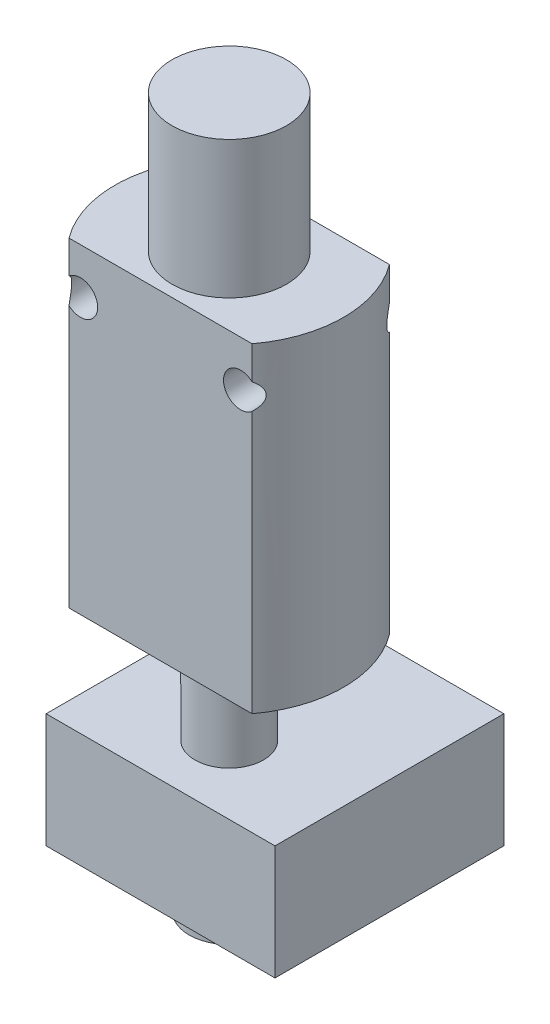
SolidWorks part; units mm, degrees
ref_plane "Plano frontal" through (0, 0, 0) normal (0, 0, 1) x (1, 0, 0)
ref_plane "Plano superior" through (0, 0, 0) normal (0, 1, 0) x (1, 0, 0)
ref_plane "Plano direito" through (0, 0, 0) normal (1, 0, 0) x (0, 0, -1)
sketch "Esboço1" plane through (0, 0, 0) normal (0, 0, 1) x (1, 0, 0)
  line L0 (0, 0) -> (0, 24.6707) construction
  line L2 (-10, 14) -> (10, 14)
  line L3 (-10, 14) -> (-10, -14)
  line L4 (-10, -14) -> (10, -14)
  line L5 (10, 14) -> (10, -14)
  line L6 (-10, 14) -> (10, -14) construction
  line L7 (-10, -14) -> (10, 14) construction
  circle A0 centre (-7, 10) radius 1.5
  circle A1 centre (7, 10) radius 1.5
  point P3 (0, 0)
  dimension "D4" = 3
  dimension "D1" = 28
  dimension "D2" = 20
  dimension "D3" = 14
  dimension "D5" = 4
extrude "Ressalto-extrusão1" add sketch "Esboço1" along normal mid plane 12
sketch "Esboço2" plane through (0, 0, 0) normal (0, 0, 1) x (1, 0, 0)
  line L0 (0, 0) -> (0, -38) construction
  line L1 (3, -33) -> (3, -23)
  line L3 (3, -33) -> (3.5, -33)
  line L4 (3.5, -33) -> (3.5, -36)
  line L5 (3.5, -36) -> (0.75, -38)
  line L6 (0.75, -38) -> (0, -38)
  line L7 (10, 14) -> (-10, 14) construction
  line L8 (3, -23) -> (3, -14)
  line L9 (-10, -14) -> (10, -14) construction
  line L10 (0, -38) -> (0, -14)
  line L11 (3, -14) -> (0, -14)
  line L12 (0, 26) -> (5, 26)
  line L13 (5, 26) -> (5, 14)
  line L14 (5, 14) -> (0, 14)
  line L15 (0, 26) -> (0, 14)
  dimension "D1" = 2
  dimension "D2" = 9
  dimension "D3" = 10
  dimension "D4" = 6
  dimension "D5" = 3
  dimension "D6" = 7
  dimension "D7" = 1.5
  dimension "D8" = 12
  dimension "D9" = 10
revolve "Revolução1" add sketch "Esboço2" angle 360 about L0
sketch "Esboço3" plane through (0, 0, 0) normal (0, 1, 0) x (1, 0, 0)
  line L0 (10, -6) -> (-10, -6) construction
  line L1 (-10, 14) -> (10, 14)
  line L2 (-10, 14) -> (-10, -6)
  line L3 (-10, -6) -> (10, -6)
  line L4 (10, 14) -> (10, -6)
  line L5 (-10, 14) -> (10, -6) construction
  line L6 (-10, -6) -> (10, 14) construction
  point P0 (0, 4)
  dimension "D1" = 20
extrude "Ressalto-extrusão2" add sketch "Esboço3" along normal blind 10 from surface at -33 starting at face at (0, -33, 3)
sketch "Esboço4" plane through (0, 14, 0) normal (0, 1, 0) x (1, 0, 0)
  line L0 (-8, 6) -> (-10, 6)
  line L1 (8, -6) -> (10, -6)
  line L4 (10, 6) -> (-10, 6)
  line L5 (-10, 6) -> (-10, -6)
  line L6 (-10, -6) -> (10, -6)
  line L7 (10, -6) -> (10, 6)
  line L8 (10, 6) -> (8, 6)
  line L9 (-10, 6) -> (-10, -6)
  line L10 (-10, -6) -> (-8, -6)
  line L11 (10, -6) -> (10, 6)
  arc A0 (-8, 6) -> (-8, -6) centre (0, 0) ccw
  arc A1 (8, -6) -> (8, 6) centre (0, 0) ccw
  line M6 (10, 6) -> (-10, 6)
  line M7 (-10, 6) -> (-10, -6)
  line M8 (-10, -6) -> (10, -6)
  line M9 (10, -6) -> (10, 6)
  dimension "D1" = 0
extrude "Corte-extrusão1" cut sketch "Esboço4" against normal up to surface (28 mm away) contours A0 M6 M7 | A0 L9 M8 | A1 M8 M9 | A1 L11 M6 up to face at (0, -14, 3)
